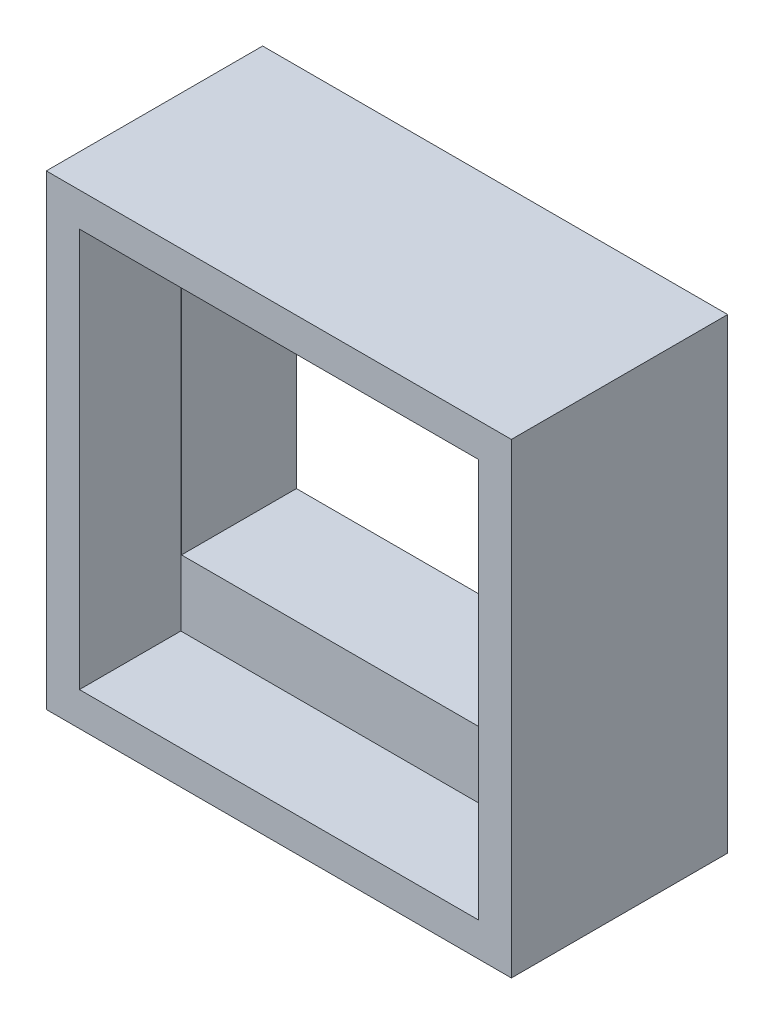
SolidWorks part; units mm, degrees
ref_plane "前基準面" through (0, 0, 0) normal (0, 0, 1) x (1, 0, 0)
ref_plane "上基準面" through (0, 0, 0) normal (0, 1, 0) x (1, 0, 0)
ref_plane "右基準面" through (0, 0, 0) normal (1, 0, 0) x (0, 0, -1)
sketch "草圖1" plane through (0, 0, 0) normal (0, 0, 1) x (1, 0, 0)
  line L1 (-28.2393, 17.713) -> (30.5607, 17.713)
  line L2 (-28.2393, 17.713) -> (-28.2393, -21.687)
  line L3 (-28.2393, -21.687) -> (30.5607, -21.687)
  line L4 (30.5607, 17.713) -> (30.5607, -21.687)
  line L5 (-33.2393, 32.513) -> (35.5607, 32.513)
  line L6 (-33.2393, 32.513) -> (-33.2393, -36.487)
  line L7 (-33.2393, -36.487) -> (35.5607, -36.487)
  line L8 (35.5607, 32.513) -> (35.5607, -36.487)
  dimension "D1" = 58.8
  dimension "D2" = 39.4
  dimension "D3" = 68.8
  dimension "D4" = 5
  dimension "D5" = 14.8
  dimension "D6" = 69
extrude "填料-伸長1" add sketch "草圖1" along normal blind 32
sketch "草圖5" plane through (0, 0, 32) normal (0, 0, 1) x (1, 0, 0)
  line L1 (-28.3393, 27.513) -> (30.6607, 27.513)
  line L2 (-28.3393, 27.513) -> (-28.3393, -31.487)
  line L3 (-28.3393, -31.487) -> (30.6607, -31.487)
  line L4 (30.6607, 27.513) -> (30.6607, -31.487)
  line L5 (-33.2393, 32.513) -> (-33.2393, -36.487) construction
  line L7 (35.5607, 32.513) -> (-33.2393, 32.513) construction
  dimension "D1" = 59
  dimension "D2" = 5
  dimension "4.1" = 4.9
  dimension "D3" = 59
extrude "除料-伸長1" cut sketch "草圖5" against normal blind 15
